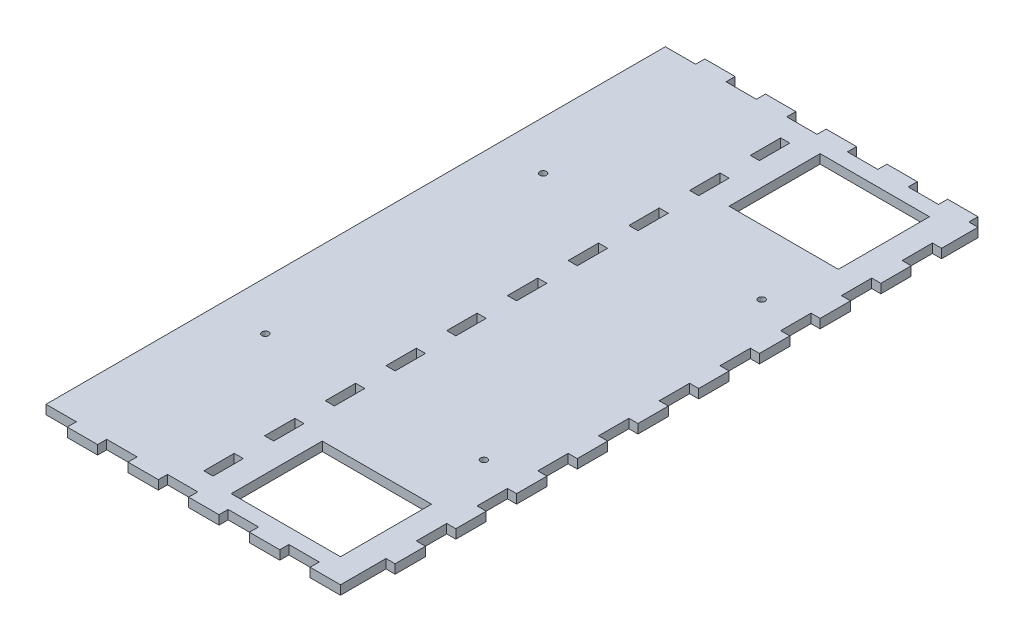
SolidWorks part; units mm, degrees
ref_plane "Front Plane" through (0, 0, 0) normal (0, 0, 1) x (1, 0, 0)
ref_plane "Top Plane" through (0, 0, 0) normal (0, 1, 0) x (1, 0, 0)
ref_plane "Right Plane" through (0, 0, 0) normal (1, 0, 0) x (0, 0, -1)
sketch "Sketch1" plane through (0, 0, 0) normal (0, 1, 0) x (1, 0, 0)
  line L1 (0, 0) -> (100, 0)
  line L2 (0, 0) -> (0, 204)
  line L3 (0, 204) -> (100, 204)
  line L4 (100, 0) -> (100, 204)
  dimension "D1" = 100
  dimension "D2" = 204
extrude "Boss-Extrude1" add sketch "Sketch1" along normal blind 3
sketch "Sketch2" plane through (0, 0, 0) normal (0, 0, 1) x (1, 0, 0)
  line L0 (0, 0) -> (100, 0) construction
  line L1 (100, 3) -> (90, 3)
  line L2 (100, 3) -> (100, 0)
  line L3 (100, 0) -> (90, 0)
  line L4 (90, 3) -> (90, 0)
  dimension "D1" = 10
extrude "Boss-Extrude2" add sketch "Sketch2" along normal blind 3
pattern_linear "LPattern1" count 5 spacing 20 along (-1, 0, 0) of "Boss-Extrude2"
sketch "Sketch3" plane through (0, 0, -204) normal (0, 0, -1) x (-1, 0, 0)
  line L1 (-100, 3) -> (-90, 3)
  line L2 (-100, 3) -> (-100, 0)
  line L3 (-100, 0) -> (-90, 0)
  line L4 (-90, 3) -> (-90, 0)
extrude "Boss-Extrude3" add sketch "Sketch3" along normal blind 3
pattern_linear "LPattern2" count 5 spacing 20 along (-1, 0, 0) of "Boss-Extrude3"
sketch "Sketch4" plane through (0, 3, 0) normal (0, 1, 0) x (1, 0, 0)
  line L0 (0, 204) -> (0, 0) construction
  line L1 (45, 7) -> (48, 7)
  line L2 (45, 7) -> (45, 17)
  line L3 (45, 17) -> (48, 17)
  line L4 (48, 7) -> (48, 17)
  line L5 (40, 0) -> (50, 0) construction
  dimension "D1" = 45
  dimension "D2" = 7
  dimension "D3" = 10
  dimension "D4" = 3
extrude "Cut-Extrude1" cut sketch "Sketch4" against normal through all
pattern_linear "LPattern3" count 10 spacing 20 along (0, 0, -1) of "Cut-Extrude1"
sketch "Sketch5" plane through (0, 3, 0) normal (0, 1, 0) x (1, 0, 0)
  line L0 (48, 7) -> (48, 17) construction
  line L1 (56, 5) -> (92, 5)
  line L2 (56, 5) -> (56, 35)
  line L3 (56, 35) -> (92, 35)
  line L4 (92, 5) -> (92, 35)
  line L5 (100, -3) -> (100, 207) construction
  line L6 (0, 102) -> (100, 102) construction
  line L7 (0, 204) -> (0, 0) construction
  line L8 (56, 169) -> (92, 169)
  line L9 (92, 199) -> (92, 169)
  line L10 (56, 199) -> (92, 199)
  line L11 (56, 199) -> (56, 169)
  line L12 (80, 0) -> (90, 0) construction
  circle A0 centre (88, 147.75) radius 1.1
  circle A1 centre (88, 56.25) radius 1.1
  circle A2 centre (16, 56.25) radius 1.1
  circle A3 centre (16, 147.75) radius 1.1
  point P6 (48, 12)
  point P19 (85, 0)
  point P28 (0, 0)
  point P29 (0, 0)
  dimension "D6" = 2.2
  dimension "D1" = 30
  dimension "D2" = 8
  dimension "D3" = 8
  dimension "D4" = 5
  dimension "D5" = 91.5
  dimension "D7" = 72
  dimension "D8" = 12
extrude "Cut-Extrude2" cut sketch "Sketch5" against normal through all
sketch "Sketch6" plane through (100, 0, 0) normal (1, 0, 0) x (0, 0, -1)
  line L0 (-3, 0) -> (207, 0) construction
  line L5 (207, 3) -> (207, 0) construction
  line L42 (-3, 3) -> (207, 3) construction
  line L83 (204, 0) -> (192, 0)
  line L84 (204, 0) -> (204, 3)
  line L85 (204, 3) -> (192, 3)
  line L86 (192, 0) -> (192, 3)
  line L87 (162, 3) -> (162, 0)
  line L88 (182, 3) -> (172, 3)
  line L89 (182, 3) -> (182, 0)
  line L90 (182, 0) -> (172, 0)
  line L91 (172, 3) -> (172, 0)
  line L92 (162, 3) -> (152, 3)
  line L93 (152, 3) -> (152, 0)
  line L94 (162, 0) -> (152, 0)
  line L95 (142, 3) -> (142, 0)
  line L96 (142, 3) -> (132, 3)
  line L97 (132, 3) -> (132, 0)
  line L98 (142, 0) -> (132, 0)
  line L99 (122, 3) -> (122, 0)
  line L100 (122, 3) -> (112, 3)
  line L101 (112, 3) -> (112, 0)
  line L102 (122, 0) -> (112, 0)
  line L103 (102, 3) -> (102, 0)
  line L104 (102, 3) -> (92, 3)
  line L105 (92, 3) -> (92, 0)
  line L106 (102, 0) -> (92, 0)
  line L107 (82, 3) -> (82, 0)
  line L108 (82, 3) -> (72, 3)
  line L109 (72, 3) -> (72, 0)
  line L110 (82, 0) -> (72, 0)
  line L111 (62, 3) -> (62, 0)
  line L112 (62, 3) -> (52, 3)
  line L113 (52, 3) -> (52, 0)
  line L114 (62, 0) -> (52, 0)
  line L115 (42, 3) -> (42, 0)
  line L116 (42, 3) -> (32, 3)
  line L117 (32, 3) -> (32, 0)
  line L118 (42, 0) -> (32, 0)
  line L119 (22, 3) -> (22, 0)
  line L120 (22, 3) -> (12, 3)
  line L121 (12, 3) -> (12, 0)
  line L122 (22, 0) -> (12, 0)
  dimension "D1" = 12
  dimension "D2" = 10
  dimension "D3" = 3
  dimension "D4" = 10
extrude "Boss-Extrude4" add sketch "Sketch6" along normal blind 3
